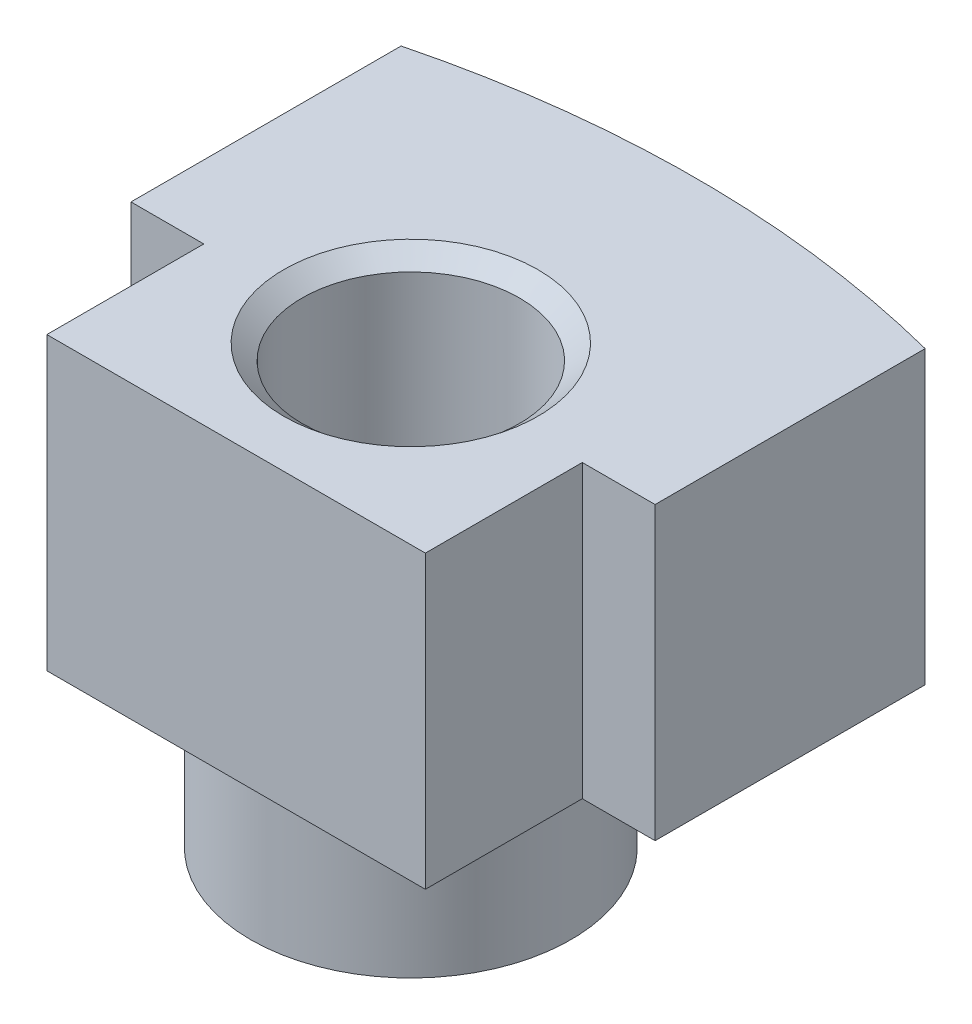
SolidWorks part; units mm, degrees
material "6061-T6 (SS)"
ref_plane "Front Plane" through (0, 0, 0) normal (0, 0, 1) x (1, 0, 0)
ref_plane "Top Plane" through (0, 0, 0) normal (0, 1, 0) x (1, 0, 0)
ref_plane "Right Plane" through (0, 0, 0) normal (1, 0, 0) x (0, 0, -1)
sketch "Sketch1" plane through (0, 0, 0) normal (0, 1, 0) x (1, 0, 0)
  line L9 (22.86, 0) -> (-22.86, 0) construction
  line L10 (0, -20.7391) -> (0, -37.2491) construction
  line L11 (15.9887, 1.4841) -> (-15.9887, 1.4841) construction
  line L12 (0, 0) -> (0, -20.7391) construction
  line L14 (0, -89.1921) -> (-15.9887, 1.4841) construction
  line L15 (0, -89.1921) -> (15.9887, 1.4841) construction
  line L17 (-15.9887, 1.4841) -> (-15.9887, 2.7541) construction
  line L24 (-16.51, -37.2491) -> (16.51, -37.2491)
  line L26 (-16.51, -37.2491) -> (0, -37.2491) construction
  line L32 (-14.2107, -18.5819) -> (-14.2107, 2.7541) construction
  line L33 (-14.2107, -18.5819) -> (-17.7667, -18.5819) construction
  line L34 (-14.2107, 2.7541) -> (-17.7667, 2.7541) construction
  line L35 (-17.7667, -18.5819) -> (-17.7667, 2.7541) construction
  line L36 (-14.2107, -18.5819) -> (-17.7667, 2.7541) construction
  line L37 (-14.2107, 2.7541) -> (-17.7667, -18.5819) construction
  line L38 (-22.86, 0) -> (-22.86, -23.5589)
  line L39 (-22.86, -23.5589) -> (-16.51, -23.5589)
  line L40 (-16.51, -23.5589) -> (-16.51, -37.2491)
  line L41 (16.51, -37.2491) -> (16.51, -23.5589)
  line L42 (16.51, -23.5589) -> (22.86, -23.5589)
  line L43 (22.86, -23.5589) -> (22.86, 0)
  arc A0 (-22.86, 0) -> (22.86, 0) centre (0, -89.1921) cw
  circle A1 centre (0, -20.7391) radius 11.049 construction
  point P3 (0, 2.8829)
  point P14 (0, -37.2491)
  point P16 (-15.9887, 2.7541)
  point P18 (-15.9887, -7.9139)
  dimension "D9" = 22.098
  dimension "D13" = 4.977
  dimension "D2" = 1.27
  dimension "D3" = 21.336
  dimension "D4" = 33.02
  dimension "D5" = 16.51
  dimension "D6" = 20
  dimension "D7" = 92.075
  dimension "D8" = 23.622
  dimension "D10" = 3.556
  dimension "D12" = 45.72
extrude "Boss-Extrude1" add sketch "Sketch1" along normal blind 25.4 contours A0 L43 L42 L41 L24 L40 L39 L38
ref_plane "Plane3" through (15.9887, 0, -1.4841) normal (0.1736, 0, -0.9848) x (-0.9848, 0, -0.1736)
sketch "Sketch21" plane through (0, 0, 0) normal (0, -1, 0) x (1, 0, 0)
  line L2 (0, 37.2491) -> (0, 22.0091) construction
  line L7 (-16.51, 37.2491) -> (16.51, 37.2491) construction
  circle A1 centre (0, 22.0091) radius 13.97
  dimension "D1" = 15.24
  dimension "D2" = 27.94
extrude "Boss-Extrude2" add sketch "Sketch21" along normal blind 12.7
hole_wizard "1/2-14 NPSM Tapped Hole1" positions "Sketch4" profile "Sketch5" tap size "1/2-14 NPSM" standard "ANSI Inch"
sketch "Sketch4" plane through (0, 25.4, 0) normal (0, 1, 0) x (1, 0, 0)
  line L0 (-16.51, -37.2491) -> (16.51, -37.2491) construction
  line L1 (-16.51, -37.2491) -> (16.51, -37.2491) construction
  line L3 (0, -37.2491) -> (0, -22.0091) construction
  point P17 (0, -22.0091)
  point P41 (0, -22.0091)
  dimension "D1" = 15.24
sketch "Sketch5" plane through (0, 25.4, 22.0091) normal (1, 0, 0) x (0, 0, 1)
  line L0 (0, 0) -> (0, 31.1003)
  line L1 (0, 31.1003) -> (9.4869, 25.4)
  line L2 (9.4869, 25.4) -> (9.4869, 1.3427)
  line L3 (9.4869, 1.3427) -> (11.0871, 0)
  line L5 (11.0871, 0) -> (0, 0)
  line L6 (-9.4869, 1.3427) -> (-11.0871, 0) construction
  line L10 (0, 31.1003) -> (-9.4869, 25.4) construction
  line L11 (0, -6.35) -> (0, 107.95) construction
  dimension "Tap Drill Dia." = 18.9738
  dimension "Tap Drill Depth" = 25.4
  dimension "Near C'Sink Dia." = 22.1742
  dimension "Near C'Sink Angle" = 100
  dimension "Drill Angle" = 118
ref_plane "Plane4" through (0, 0, -1.4841) normal (0, 0, 1) x (1, 0, 0)
ref_plane "Plane5" through (0, 0, -2.7541) normal (0, 0, 1) x (1, 0, 0)
hole_wizard "Tap Drill for #8-32 Tap1" positions "Sketch25" profile "Sketch26" hole size "#8-32" standard "ANSI Inch"
sketch "Sketch25" plane through (0, 0, -2.7541) normal (0, 0, 1) x (1, 0, 0)
  line L0 (-15.9887, 12.7) -> (-15.9887, 0) construction
  point P0 (-15.9887, 12.7)
  dimension "D1" = 12.7
sketch "Sketch26" plane through (-15.9887, 12.7, -2.7541) normal (1, 0, 0) x (0, 1, 0)
  line L0 (0, 0) -> (0, 22.3738)
  line L1 (0, 22.3738) -> (1.7272, 21.336)
  line L2 (1.7272, 21.336) -> (1.7272, 0)
  line L5 (1.7272, 0) -> (0, 0)
  line L10 (0, 22.3738) -> (-1.7272, 21.336) construction
  line L11 (0, -6.35) -> (0, 107.95) construction
  dimension "Hole Dia." = 3.4544
  dimension "Hole Depth" = 21.336
  dimension "Drill Angle" = 118
mirror "Mirror1" about plane through (0, 0, 0) normal (1, 0, 0) of "Tap Drill for #8-32 Tap1"
